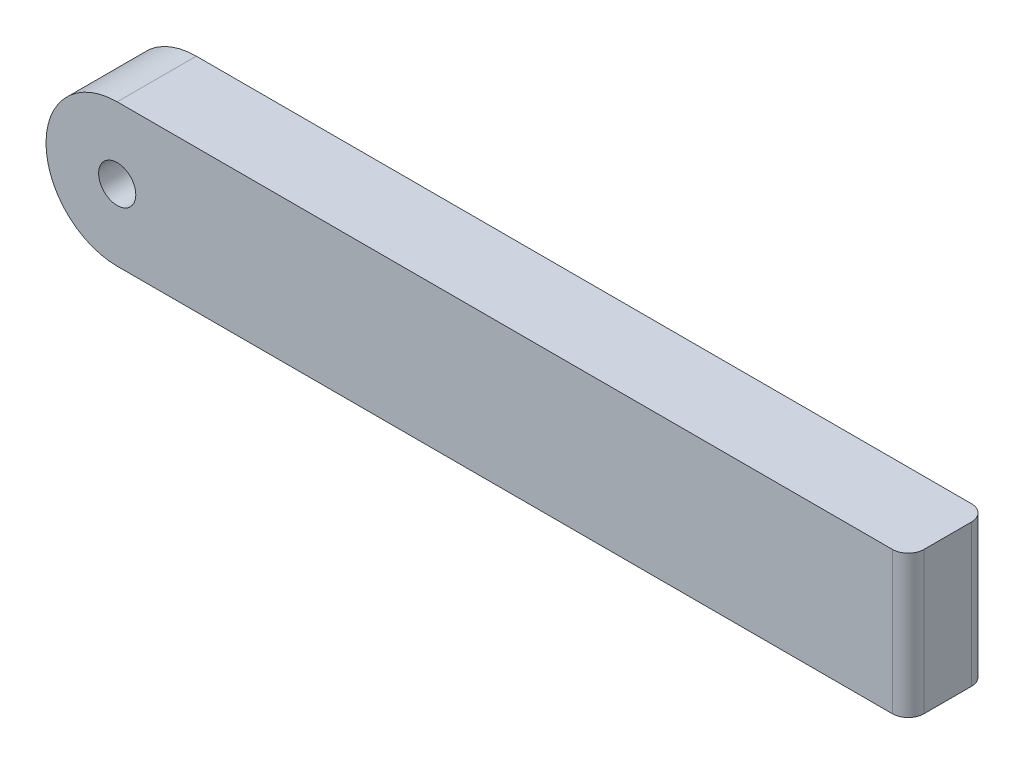
SolidWorks part; units mm, degrees
ref_plane "Plan de face" through (0, 0, 0) normal (0, 0, 1) x (1, 0, 0)
ref_plane "Plan de dessus" through (0, 0, 0) normal (0, 1, 0) x (1, 0, 0)
ref_plane "Plan de droite" through (0, 0, 0) normal (1, 0, 0) x (0, 0, -1)
sketch "Esquisse1" plane through (0, 0, 0) normal (0, 0, 1) x (1, 0, 0)
  line L1 (0, 9) -> (100, 9)
  line L2 (0, 9) -> (0, -9) construction
  line L3 (0, -9) -> (100, -9)
  line L4 (100, 9) -> (100, -9)
  arc A0 (0, 9) -> (0, -9) centre (0, 0) ccw
  circle A1 centre (0, 0) radius 2.35
  dimension "D2" = 4.7
  dimension "D3" = 100
  dimension "D4" = 18
extrude "Boss.-Extru.1" add sketch "Esquisse1" along normal blind 10
fillet "Congé1" radius 2 2 edges at (100, 0, 0) (100, 0, 10)
